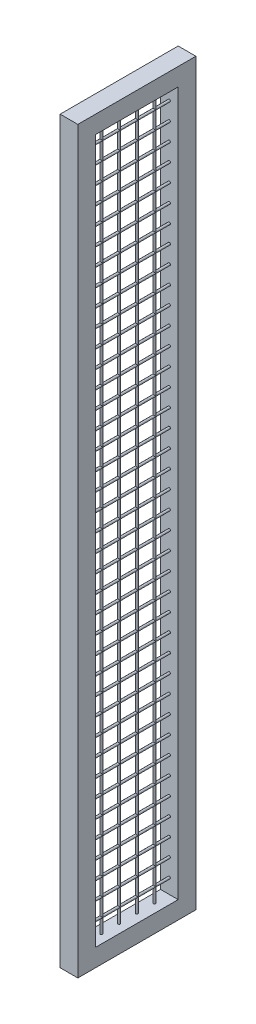
SolidWorks part; units mm, degrees
ref_plane "Piano frontale" through (0, 0, 0) normal (0, 0, 1) x (1, 0, 0)
ref_plane "Piano superiore" through (0, 0, 0) normal (0, 1, 0) x (1, 0, 0)
ref_plane "Piano destro" through (0, 0, 0) normal (1, 0, 0) x (0, 0, -1)
sketch "Schizzo1" plane through (0, 0, 0) normal (0, 0, 1) x (1, 0, 0)
  line L0 (-50, 50) -> (50, 50) construction
  line L1 (-30, 50) -> (30, 50)
  line L2 (-30, 50) -> (-30, 110)
  line L3 (-30, 110) -> (30, 110)
  line L4 (30, 50) -> (30, 110)
  line L5 (-50, 50) -> (-50, 2495) construction
  line L6 (-50, 2555) -> (50, 2555) construction
  line L7 (-30, 2555) -> (30, 2555)
  line L8 (-30, 2555) -> (-30, 2495)
  line L9 (-30, 2495) -> (30, 2495)
  line L10 (30, 2555) -> (30, 2495)
  circle A0 centre (0, 160) radius 3.75
  circle A1 centre (0, 220) radius 3.75
  circle A2 centre (0, 280) radius 3.75
  circle A3 centre (0, 340) radius 3.75
  circle A4 centre (0, 400) radius 3.75
  circle A5 centre (0, 460) radius 3.75
  circle A6 centre (0, 520) radius 3.75
  circle A7 centre (0, 580) radius 3.75
  circle A8 centre (0, 640) radius 3.75
  circle A9 centre (0, 700) radius 3.75
  circle A10 centre (0, 760) radius 3.75
  circle A11 centre (0, 820) radius 3.75
  circle A12 centre (0, 880) radius 3.75
  circle A13 centre (0, 940) radius 3.75
  circle A14 centre (0, 1000) radius 3.75
  circle A15 centre (0, 1060) radius 3.75
  circle A16 centre (0, 1120) radius 3.75
  circle A17 centre (0, 1180) radius 3.75
  circle A18 centre (0, 1240) radius 3.75
  circle A19 centre (0, 1300) radius 3.75
  circle A20 centre (0, 1360) radius 3.75
  circle A21 centre (0, 1420) radius 3.75
  circle A22 centre (0, 1480) radius 3.75
  circle A23 centre (0, 1540) radius 3.75
  circle A24 centre (0, 1600) radius 3.75
  circle A25 centre (0, 1660) radius 3.75
  circle A26 centre (0, 1720) radius 3.75
  circle A27 centre (0, 1780) radius 3.75
  circle A28 centre (0, 1840) radius 3.75
  circle A29 centre (0, 1900) radius 3.75
  circle A30 centre (0, 1960) radius 3.75
  circle A31 centre (0, 2020) radius 3.75
  circle A32 centre (0, 2080) radius 3.75
  circle A33 centre (0, 2140) radius 3.75
  circle A34 centre (0, 2200) radius 3.75
  circle A35 centre (0, 2260) radius 3.75
  circle A36 centre (0, 2320) radius 3.75
  circle A37 centre (0, 2380) radius 3.75
  circle A38 centre (0, 2440) radius 3.75
  dimension "D2" = 50
  dimension "D1" = 20
  dimension "D3" = 39
extrude "Estrusione-Estrusione1" add sketch "Schizzo1" along normal blind 400
sketch "Schizzo2" plane through (0, 2555, 0) normal (0, 1, 0) x (1, 0, 0)
  line L0 (30, -400) -> (30, 0) construction
  line L1 (-30, 0) -> (30, 0)
  line L2 (-30, 0) -> (-30, -60)
  line L3 (-30, -60) -> (30, -60)
  line L4 (30, 0) -> (30, -60)
  line L5 (0, -110) -> (0, -170) construction
  line L6 (-30, -400) -> (30, -400)
  line L7 (-30, -400) -> (-30, -340)
  line L8 (-30, -340) -> (30, -340)
  line L9 (30, -400) -> (30, -340)
  circle A0 centre (0, -110) radius 3.75
  circle A1 centre (0, -170) radius 3.75
  circle A2 centre (0, -230) radius 3.75
  circle A3 centre (0, -290) radius 3.75
  circle A5 centre (0, -350) radius 3.75 [skipped]
  dimension "D1" = 50
  dimension "D2" = 5
  dimension "D3" = 60
extrude "Estrusione-Estrusione2" add sketch "Schizzo2" against normal up to surface (2445 mm away) up to face at (0, 110, 200)
